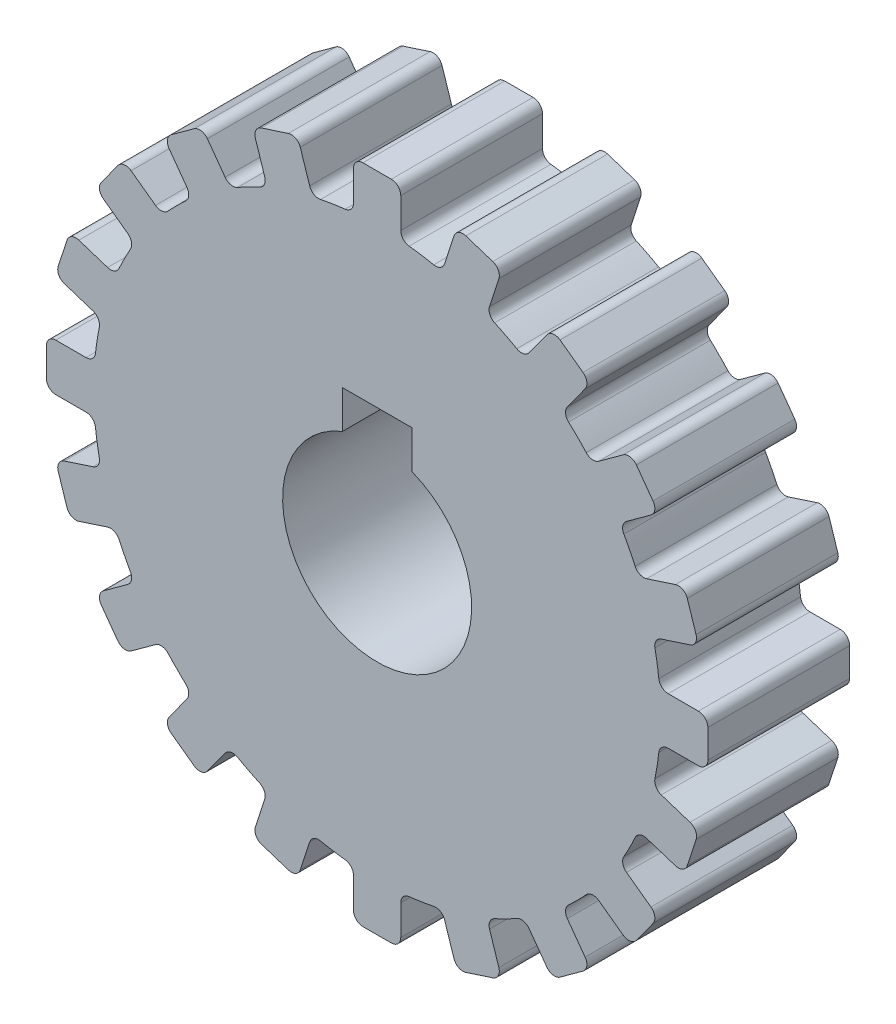
SolidWorks part; units mm, degrees
ref_plane "Front Plane" through (0, 0, 0) normal (0, 0, 1) x (1, 0, 0)
ref_plane "Top Plane" through (0, 0, 0) normal (0, 1, 0) x (1, 0, 0)
ref_plane "Right Plane" through (0, 0, 0) normal (1, 0, 0) x (0, 0, -1)
sketch "Sketch1" plane through (0, 0, 0) normal (0, 0, 1) x (1, 0, 0)
  line L0 (8.3248, 68.5416) -> (7.8409, 65.4868)
  line L1 (-1.5, 70) -> (1.5, 70)
  line L2 (2.5, 69) -> (2.5, 65.9071)
  line L3 (-2.5, 69) -> (-2.5, 65.9071)
  line L4 (9.4689, 69.3728) -> (12.4319, 68.9035)
  line L5 (13.2632, 67.7594) -> (12.7794, 64.7046)
  line L6 (18.9445, 66.3954) -> (17.9888, 63.4539)
  line L7 (20.2046, 67.0375) -> (23.0578, 66.1104)
  line L8 (23.6998, 64.8504) -> (22.7441, 61.9089)
  line L9 (29.0978, 62.6144) -> (27.6937, 59.8587)
  line L10 (30.4428, 63.0514) -> (33.1158, 61.6895)
  line L11 (33.5529, 60.3445) -> (32.1487, 57.5887)
  line L12 (38.5346, 57.2916) -> (36.7167, 54.7895)
  line L13 (39.9314, 57.5129) -> (42.3585, 55.7495)
  line L14 (42.5797, 54.3527) -> (40.7618, 51.8505)
  line L15 (47.0226, 50.5581) -> (44.8356, 48.3711)
  line L16 (48.4368, 50.5581) -> (50.5581, 48.4368)
  line L17 (50.5581, 47.0226) -> (48.3711, 44.8356)
  line L18 (54.3527, 42.5797) -> (51.8505, 40.7618)
  line L19 (55.7495, 42.3585) -> (57.5129, 39.9314)
  line L20 (57.2916, 38.5346) -> (54.7895, 36.7167)
  line L21 (60.3445, 33.5529) -> (57.5887, 32.1487)
  line L22 (61.6895, 33.1158) -> (63.0514, 30.4428)
  line L23 (62.6144, 29.0978) -> (59.8587, 27.6937)
  line L24 (64.8504, 23.6998) -> (61.9089, 22.7441)
  line L25 (66.1104, 23.0578) -> (67.0375, 20.2046)
  line L26 (66.3954, 18.9445) -> (63.4539, 17.9888)
  line L27 (67.7594, 13.2632) -> (64.7046, 12.7794)
  line L28 (68.9035, 12.4319) -> (69.3728, 9.4689)
  line L29 (68.5416, 8.3248) -> (65.4868, 7.8409)
  line L30 (69, 2.5) -> (65.9071, 2.5)
  line L31 (70, 1.5) -> (70, -1.5)
  line L32 (69, -2.5) -> (65.9071, -2.5)
  line L33 (68.5416, -8.3248) -> (65.4868, -7.8409)
  line L34 (69.3728, -9.4689) -> (68.9035, -12.4319)
  line L35 (67.7594, -13.2632) -> (64.7046, -12.7794)
  line L36 (66.3954, -18.9445) -> (63.4539, -17.9888)
  line L37 (67.0375, -20.2046) -> (66.1104, -23.0578)
  line L38 (64.8504, -23.6998) -> (61.9089, -22.7441)
  line L39 (62.6144, -29.0978) -> (59.8587, -27.6937)
  line L40 (63.0514, -30.4428) -> (61.6895, -33.1158)
  line L41 (60.3445, -33.5529) -> (57.5887, -32.1487)
  line L42 (57.2916, -38.5346) -> (54.7895, -36.7167)
  line L43 (57.5129, -39.9314) -> (55.7495, -42.3585)
  line L44 (54.3527, -42.5797) -> (51.8505, -40.7618)
  line L45 (50.5581, -47.0226) -> (48.3711, -44.8356)
  line L46 (50.5581, -48.4368) -> (48.4368, -50.5581)
  line L47 (47.0226, -50.5581) -> (44.8356, -48.3711)
  line L48 (42.5797, -54.3527) -> (40.7618, -51.8505)
  line L49 (42.3585, -55.7495) -> (39.9314, -57.5129)
  line L50 (38.5346, -57.2916) -> (36.7167, -54.7895)
  line L51 (33.5529, -60.3445) -> (32.1487, -57.5887)
  line L52 (33.1158, -61.6895) -> (30.4428, -63.0514)
  line L53 (29.0978, -62.6144) -> (27.6937, -59.8587)
  line L54 (23.6998, -64.8504) -> (22.7441, -61.9089)
  line L55 (23.0578, -66.1104) -> (20.2046, -67.0375)
  line L56 (18.9445, -66.3954) -> (17.9888, -63.4539)
  line L57 (13.2632, -67.7594) -> (12.7794, -64.7046)
  line L58 (12.4319, -68.9035) -> (9.4689, -69.3728)
  line L59 (8.3248, -68.5416) -> (7.8409, -65.4868)
  line L60 (2.5, -69) -> (2.5, -65.9071)
  line L61 (1.5, -70) -> (-1.5, -70)
  line L62 (-2.5, -69) -> (-2.5, -65.9071)
  line L63 (-8.3248, -68.5416) -> (-7.8409, -65.4868)
  line L64 (-9.4689, -69.3728) -> (-12.4319, -68.9035)
  line L65 (-13.2632, -67.7594) -> (-12.7794, -64.7046)
  line L66 (-18.9445, -66.3954) -> (-17.9888, -63.4539)
  line L67 (-20.2046, -67.0375) -> (-23.0578, -66.1104)
  line L68 (-23.6998, -64.8504) -> (-22.7441, -61.9089)
  line L69 (-29.0978, -62.6144) -> (-27.6937, -59.8587)
  line L70 (-30.4428, -63.0514) -> (-33.1158, -61.6895)
  line L71 (-33.5529, -60.3445) -> (-32.1487, -57.5887)
  line L72 (-38.5346, -57.2916) -> (-36.7167, -54.7895)
  line L73 (-39.9314, -57.5129) -> (-42.3585, -55.7495)
  line L74 (-42.5797, -54.3527) -> (-40.7618, -51.8505)
  line L75 (-47.0226, -50.5581) -> (-44.8356, -48.3711)
  line L76 (-48.4368, -50.5581) -> (-50.5581, -48.4368)
  line L77 (-50.5581, -47.0226) -> (-48.3711, -44.8356)
  line L78 (-54.3527, -42.5797) -> (-51.8505, -40.7618)
  line L79 (-55.7495, -42.3585) -> (-57.5129, -39.9314)
  line L80 (-57.2916, -38.5346) -> (-54.7895, -36.7167)
  line L81 (-60.3445, -33.5529) -> (-57.5887, -32.1487)
  line L82 (-61.6895, -33.1158) -> (-63.0514, -30.4428)
  line L83 (-62.6144, -29.0978) -> (-59.8587, -27.6937)
  line L84 (-64.8504, -23.6998) -> (-61.9089, -22.7441)
  line L85 (-66.1104, -23.0578) -> (-67.0375, -20.2046)
  line L86 (-66.3954, -18.9445) -> (-63.4539, -17.9888)
  line L87 (-67.7594, -13.2632) -> (-64.7046, -12.7794)
  line L88 (-68.9035, -12.4319) -> (-69.3728, -9.4689)
  line L89 (-68.5416, -8.3248) -> (-65.4868, -7.8409)
  line L90 (-69, -2.5) -> (-65.9071, -2.5)
  line L91 (-70, -1.5) -> (-70, 1.5)
  line L92 (-69, 2.5) -> (-65.9071, 2.5)
  line L93 (-68.5416, 8.3248) -> (-65.4868, 7.8409)
  line L94 (-69.3728, 9.4689) -> (-68.9035, 12.4319)
  line L95 (-67.7594, 13.2632) -> (-64.7046, 12.7794)
  line L96 (-66.3954, 18.9445) -> (-63.4539, 17.9888)
  line L97 (-67.0375, 20.2046) -> (-66.1104, 23.0578)
  line L98 (-64.8504, 23.6998) -> (-61.9089, 22.7441)
  line L99 (-62.6144, 29.0978) -> (-59.8587, 27.6937)
  line L100 (-63.0514, 30.4428) -> (-61.6895, 33.1158)
  line L101 (-60.3445, 33.5529) -> (-57.5887, 32.1487)
  line L102 (-57.2916, 38.5346) -> (-54.7895, 36.7167)
  line L103 (-57.5129, 39.9314) -> (-55.7495, 42.3585)
  line L104 (-54.3527, 42.5797) -> (-51.8505, 40.7618)
  line L105 (-50.5581, 47.0226) -> (-48.3711, 44.8356)
  line L106 (-50.5581, 48.4368) -> (-48.4368, 50.5581)
  line L107 (-47.0226, 50.5581) -> (-44.8356, 48.3711)
  line L108 (-42.5797, 54.3527) -> (-40.7618, 51.8505)
  line L109 (-42.3585, 55.7495) -> (-39.9314, 57.5129)
  line L110 (-38.5346, 57.2916) -> (-36.7167, 54.7895)
  line L111 (-33.5529, 60.3445) -> (-32.1487, 57.5887)
  line L112 (-33.1158, 61.6895) -> (-30.4428, 63.0514)
  line L113 (-29.0978, 62.6144) -> (-27.6937, 59.8587)
  line L114 (-23.6998, 64.8504) -> (-22.7441, 61.9089)
  line L115 (-23.0578, 66.1104) -> (-20.2046, 67.0375)
  line L116 (-18.9445, 66.3954) -> (-17.9888, 63.4539)
  line L117 (-13.2632, 67.7594) -> (-12.7794, 64.7046)
  line L118 (-12.4319, 68.9035) -> (-9.4689, 69.3728)
  line L119 (-8.3248, 68.5416) -> (-7.8409, 65.4868)
  arc A0 (-3.447, 64.9085) -> (-6.7494, 64.6486) centre (0, 0) ccw
  arc A2 (-2.5, 65.9071) -> (-3.447, 64.9085) centre (-3.5, 65.9071) cw
  arc A3 (3.447, 64.9085) -> (2.5, 65.9071) centre (3.5, 65.9071) cw
  arc A4 (1.5, 70) -> (2.5, 69) centre (1.5, 69) cw
  arc A5 (-1.5, 70) -> (-2.5, 69) centre (-1.5, 69) ccw
  arc A6 (7.8409, 65.4868) -> (6.7494, 64.6486) centre (6.8532, 65.6432) cw
  arc A7 (9.4689, 69.3728) -> (8.3248, 68.5416) centre (9.3124, 68.3851) ccw
  arc A8 (12.4319, 68.9035) -> (13.2632, 67.7594) centre (12.2755, 67.9158) cw
  arc A9 (13.5585, 63.5702) -> (12.7794, 64.7046) centre (13.7671, 64.5482) cw
  arc A10 (17.9888, 63.4539) -> (16.7796, 62.7969) centre (17.0377, 63.763) cw
  arc A11 (20.2046, 67.0375) -> (18.9445, 66.3954) centre (19.8956, 66.0864) ccw
  arc A12 (23.0578, 66.1104) -> (23.6998, 64.8504) centre (22.7488, 65.1594) cw
  arc A13 (23.3361, 60.6665) -> (22.7441, 61.9089) centre (23.6951, 61.5998) cw
  arc A14 (27.6937, 59.8587) -> (26.3966, 59.3988) centre (26.8027, 60.3127) cw
  arc A15 (30.4428, 63.0514) -> (29.0978, 62.6144) centre (29.9888, 62.1604) ccw
  arc A16 (33.1158, 61.6895) -> (33.5529, 60.3445) centre (32.6619, 60.7985) cw
  arc A17 (32.5391, 56.269) -> (32.1487, 57.5887) centre (33.0397, 57.1347) cw
  arc A18 (36.7167, 54.7895) -> (35.3636, 54.5382) centre (35.9077, 55.3772) cw
  arc A19 (39.9314, 57.5129) -> (38.5346, 57.2916) centre (39.3437, 56.7039) ccw
  arc A20 (42.3585, 55.7495) -> (42.5797, 54.3527) centre (41.7707, 54.9405) cw
  arc A21 (40.9409, 50.486) -> (40.7618, 51.8505) centre (41.5708, 51.2627) cw
  arc A22 (44.8356, 48.3711) -> (43.4599, 48.3346) centre (44.1285, 49.0783) cw
  arc A23 (48.4368, 50.5581) -> (47.0226, 50.5581) centre (47.7297, 49.851) ccw
  arc A24 (50.5581, 48.4368) -> (50.5581, 47.0226) centre (49.851, 47.7297) cw
  arc A25 (48.3346, 43.4599) -> (48.3711, 44.8356) centre (49.0783, 44.1285) cw
  arc A26 (51.8505, 40.7618) -> (50.486, 40.9409) centre (51.2627, 41.5708) cw
  arc A27 (55.7495, 42.3585) -> (54.3527, 42.5797) centre (54.9405, 41.7707) ccw
  arc A28 (57.5129, 39.9314) -> (57.2916, 38.5346) centre (56.7039, 39.3437) cw
  arc A29 (54.5382, 35.3636) -> (54.7895, 36.7167) centre (55.3772, 35.9077) cw
  arc A30 (57.5887, 32.1487) -> (56.269, 32.5391) centre (57.1347, 33.0397) cw
  arc A31 (61.6895, 33.1158) -> (60.3445, 33.5529) centre (60.7985, 32.6619) ccw
  arc A32 (63.0514, 30.4428) -> (62.6144, 29.0978) centre (62.1604, 29.9888) cw
  arc A33 (59.3988, 26.3966) -> (59.8587, 27.6937) centre (60.3127, 26.8027) cw
  arc A34 (61.9089, 22.7441) -> (60.6665, 23.3361) centre (61.5998, 23.6951) cw
  arc A35 (66.1104, 23.0578) -> (64.8504, 23.6998) centre (65.1594, 22.7488) ccw
  arc A36 (67.0375, 20.2046) -> (66.3954, 18.9445) centre (66.0864, 19.8956) cw
  arc A37 (62.7969, 16.7796) -> (63.4539, 17.9888) centre (63.763, 17.0377) cw
  arc A38 (64.7046, 12.7794) -> (63.5702, 13.5585) centre (64.5482, 13.7671) cw
  arc A39 (68.9035, 12.4319) -> (67.7594, 13.2632) centre (67.9158, 12.2755) ccw
  arc A40 (69.3728, 9.4689) -> (68.5416, 8.3248) centre (68.3851, 9.3124) cw
  arc A41 (64.6486, 6.7494) -> (65.4868, 7.8409) centre (65.6432, 6.8532) cw
  arc A42 (65.9071, 2.5) -> (64.9085, 3.447) centre (65.9071, 3.5) cw
  arc A43 (70, 1.5) -> (69, 2.5) centre (69, 1.5) ccw
  arc A44 (70, -1.5) -> (69, -2.5) centre (69, -1.5) cw
  arc A45 (64.9085, -3.447) -> (65.9071, -2.5) centre (65.9071, -3.5) cw
  arc A46 (65.4868, -7.8409) -> (64.6486, -6.7494) centre (65.6432, -6.8532) cw
  arc A47 (69.3728, -9.4689) -> (68.5416, -8.3248) centre (68.3851, -9.3124) ccw
  arc A48 (68.9035, -12.4319) -> (67.7594, -13.2632) centre (67.9158, -12.2755) cw
  arc A49 (63.5702, -13.5585) -> (64.7046, -12.7794) centre (64.5482, -13.7671) cw
  arc A50 (63.4539, -17.9888) -> (62.7969, -16.7796) centre (63.763, -17.0377) cw
  arc A51 (67.0375, -20.2046) -> (66.3954, -18.9445) centre (66.0864, -19.8956) ccw
  arc A52 (66.1104, -23.0578) -> (64.8504, -23.6998) centre (65.1594, -22.7488) cw
  arc A53 (60.6665, -23.3361) -> (61.9089, -22.7441) centre (61.5998, -23.6951) cw
  arc A54 (59.8587, -27.6937) -> (59.3988, -26.3966) centre (60.3127, -26.8027) cw
  arc A55 (63.0514, -30.4428) -> (62.6144, -29.0978) centre (62.1604, -29.9888) ccw
  arc A56 (61.6895, -33.1158) -> (60.3445, -33.5529) centre (60.7985, -32.6619) cw
  arc A57 (56.269, -32.5391) -> (57.5887, -32.1487) centre (57.1347, -33.0397) cw
  arc A58 (54.7895, -36.7167) -> (54.5382, -35.3636) centre (55.3772, -35.9077) cw
  arc A59 (57.5129, -39.9314) -> (57.2916, -38.5346) centre (56.7039, -39.3437) ccw
  arc A60 (55.7495, -42.3585) -> (54.3527, -42.5797) centre (54.9405, -41.7707) cw
  arc A61 (50.486, -40.9409) -> (51.8505, -40.7618) centre (51.2627, -41.5708) cw
  arc A62 (48.3711, -44.8356) -> (48.3346, -43.4599) centre (49.0783, -44.1285) cw
  arc A63 (50.5581, -48.4368) -> (50.5581, -47.0226) centre (49.851, -47.7297) ccw
  arc A64 (48.4368, -50.5581) -> (47.0226, -50.5581) centre (47.7297, -49.851) cw
  arc A65 (43.4599, -48.3346) -> (44.8356, -48.3711) centre (44.1285, -49.0783) cw
  arc A66 (40.7618, -51.8505) -> (40.9409, -50.486) centre (41.5708, -51.2627) cw
  arc A67 (42.3585, -55.7495) -> (42.5797, -54.3527) centre (41.7707, -54.9405) ccw
  arc A68 (39.9314, -57.5129) -> (38.5346, -57.2916) centre (39.3437, -56.7039) cw
  arc A69 (35.3636, -54.5382) -> (36.7167, -54.7895) centre (35.9077, -55.3772) cw
  arc A70 (32.1487, -57.5887) -> (32.5391, -56.269) centre (33.0397, -57.1347) cw
  arc A71 (33.1158, -61.6895) -> (33.5529, -60.3445) centre (32.6619, -60.7985) ccw
  arc A72 (30.4428, -63.0514) -> (29.0978, -62.6144) centre (29.9888, -62.1604) cw
  arc A73 (26.3966, -59.3988) -> (27.6937, -59.8587) centre (26.8027, -60.3127) cw
  arc A74 (22.7441, -61.9089) -> (23.3361, -60.6665) centre (23.6951, -61.5998) cw
  arc A75 (23.0578, -66.1104) -> (23.6998, -64.8504) centre (22.7488, -65.1594) ccw
  arc A76 (20.2046, -67.0375) -> (18.9445, -66.3954) centre (19.8956, -66.0864) cw
  arc A77 (16.7796, -62.7969) -> (17.9888, -63.4539) centre (17.0377, -63.763) cw
  arc A78 (12.7794, -64.7046) -> (13.5585, -63.5702) centre (13.7671, -64.5482) cw
  arc A79 (12.4319, -68.9035) -> (13.2632, -67.7594) centre (12.2755, -67.9158) ccw
  arc A80 (9.4689, -69.3728) -> (8.3248, -68.5416) centre (9.3124, -68.3851) cw
  arc A81 (6.7494, -64.6486) -> (7.8409, -65.4868) centre (6.8532, -65.6432) cw
  arc A82 (2.5, -65.9071) -> (3.447, -64.9085) centre (3.5, -65.9071) cw
  arc A83 (1.5, -70) -> (2.5, -69) centre (1.5, -69) ccw
  arc A84 (-1.5, -70) -> (-2.5, -69) centre (-1.5, -69) cw
  arc A85 (-3.447, -64.9085) -> (-2.5, -65.9071) centre (-3.5, -65.9071) cw
  arc A86 (-7.8409, -65.4868) -> (-6.7494, -64.6486) centre (-6.8532, -65.6432) cw
  arc A87 (-9.4689, -69.3728) -> (-8.3248, -68.5416) centre (-9.3124, -68.3851) ccw
  arc A88 (-12.4319, -68.9035) -> (-13.2632, -67.7594) centre (-12.2755, -67.9158) cw
  arc A89 (-13.5585, -63.5702) -> (-12.7794, -64.7046) centre (-13.7671, -64.5482) cw
  arc A90 (-17.9888, -63.4539) -> (-16.7796, -62.7969) centre (-17.0377, -63.763) cw
  arc A91 (-20.2046, -67.0375) -> (-18.9445, -66.3954) centre (-19.8956, -66.0864) ccw
  arc A92 (-23.0578, -66.1104) -> (-23.6998, -64.8504) centre (-22.7488, -65.1594) cw
  arc A93 (-23.3361, -60.6665) -> (-22.7441, -61.9089) centre (-23.6951, -61.5998) cw
  arc A94 (-27.6937, -59.8587) -> (-26.3966, -59.3988) centre (-26.8027, -60.3127) cw
  arc A95 (-30.4428, -63.0514) -> (-29.0978, -62.6144) centre (-29.9888, -62.1604) ccw
  arc A96 (-33.1158, -61.6895) -> (-33.5529, -60.3445) centre (-32.6619, -60.7985) cw
  arc A97 (-32.5391, -56.269) -> (-32.1487, -57.5887) centre (-33.0397, -57.1347) cw
  arc A98 (-36.7167, -54.7895) -> (-35.3636, -54.5382) centre (-35.9077, -55.3772) cw
  arc A99 (-39.9314, -57.5129) -> (-38.5346, -57.2916) centre (-39.3437, -56.7039) ccw
  arc A100 (-42.3585, -55.7495) -> (-42.5797, -54.3527) centre (-41.7707, -54.9405) cw
  arc A101 (-40.9409, -50.486) -> (-40.7618, -51.8505) centre (-41.5708, -51.2627) cw
  arc A102 (-44.8356, -48.3711) -> (-43.4599, -48.3346) centre (-44.1285, -49.0783) cw
  arc A103 (-48.4368, -50.5581) -> (-47.0226, -50.5581) centre (-47.7297, -49.851) ccw
  arc A104 (-50.5581, -48.4368) -> (-50.5581, -47.0226) centre (-49.851, -47.7297) cw
  arc A105 (-48.3346, -43.4599) -> (-48.3711, -44.8356) centre (-49.0783, -44.1285) cw
  arc A106 (-51.8505, -40.7618) -> (-50.486, -40.9409) centre (-51.2627, -41.5708) cw
  arc A107 (-55.7495, -42.3585) -> (-54.3527, -42.5797) centre (-54.9405, -41.7707) ccw
  arc A108 (-57.5129, -39.9314) -> (-57.2916, -38.5346) centre (-56.7039, -39.3437) cw
  arc A109 (-54.5382, -35.3636) -> (-54.7895, -36.7167) centre (-55.3772, -35.9077) cw
  arc A110 (-57.5887, -32.1487) -> (-56.269, -32.5391) centre (-57.1347, -33.0397) cw
  arc A111 (-61.6895, -33.1158) -> (-60.3445, -33.5529) centre (-60.7985, -32.6619) ccw
  arc A112 (-63.0514, -30.4428) -> (-62.6144, -29.0978) centre (-62.1604, -29.9888) cw
  arc A113 (-59.3988, -26.3966) -> (-59.8587, -27.6937) centre (-60.3127, -26.8027) cw
  arc A114 (-61.9089, -22.7441) -> (-60.6665, -23.3361) centre (-61.5998, -23.6951) cw
  arc A115 (-66.1104, -23.0578) -> (-64.8504, -23.6998) centre (-65.1594, -22.7488) ccw
  arc A116 (-67.0375, -20.2046) -> (-66.3954, -18.9445) centre (-66.0864, -19.8956) cw
  arc A117 (-62.7969, -16.7796) -> (-63.4539, -17.9888) centre (-63.763, -17.0377) cw
  arc A118 (-64.7046, -12.7794) -> (-63.5702, -13.5585) centre (-64.5482, -13.7671) cw
  arc A119 (-68.9035, -12.4319) -> (-67.7594, -13.2632) centre (-67.9158, -12.2755) ccw
  arc A120 (-69.3728, -9.4689) -> (-68.5416, -8.3248) centre (-68.3851, -9.3124) cw
  arc A121 (-64.6486, -6.7494) -> (-65.4868, -7.8409) centre (-65.6432, -6.8532) cw
  arc A122 (-65.9071, -2.5) -> (-64.9085, -3.447) centre (-65.9071, -3.5) cw
  arc A123 (-70, -1.5) -> (-69, -2.5) centre (-69, -1.5) ccw
  arc A124 (-70, 1.5) -> (-69, 2.5) centre (-69, 1.5) cw
  arc A125 (-64.9085, 3.447) -> (-65.9071, 2.5) centre (-65.9071, 3.5) cw
  arc A126 (-65.4868, 7.8409) -> (-64.6486, 6.7494) centre (-65.6432, 6.8532) cw
  arc A127 (-69.3728, 9.4689) -> (-68.5416, 8.3248) centre (-68.3851, 9.3124) ccw
  arc A128 (-68.9035, 12.4319) -> (-67.7594, 13.2632) centre (-67.9158, 12.2755) cw
  arc A129 (-63.5702, 13.5585) -> (-64.7046, 12.7794) centre (-64.5482, 13.7671) cw
  arc A130 (-63.4539, 17.9888) -> (-62.7969, 16.7796) centre (-63.763, 17.0377) cw
  arc A131 (-67.0375, 20.2046) -> (-66.3954, 18.9445) centre (-66.0864, 19.8956) ccw
  arc A132 (-66.1104, 23.0578) -> (-64.8504, 23.6998) centre (-65.1594, 22.7488) cw
  arc A133 (-60.6665, 23.3361) -> (-61.9089, 22.7441) centre (-61.5998, 23.6951) cw
  arc A134 (-59.8587, 27.6937) -> (-59.3988, 26.3966) centre (-60.3127, 26.8027) cw
  arc A135 (-63.0514, 30.4428) -> (-62.6144, 29.0978) centre (-62.1604, 29.9888) ccw
  arc A136 (-61.6895, 33.1158) -> (-60.3445, 33.5529) centre (-60.7985, 32.6619) cw
  arc A137 (-56.269, 32.5391) -> (-57.5887, 32.1487) centre (-57.1347, 33.0397) cw
  arc A138 (-54.7895, 36.7167) -> (-54.5382, 35.3636) centre (-55.3772, 35.9077) cw
  arc A139 (-57.5129, 39.9314) -> (-57.2916, 38.5346) centre (-56.7039, 39.3437) ccw
  arc A140 (-55.7495, 42.3585) -> (-54.3527, 42.5797) centre (-54.9405, 41.7707) cw
  arc A141 (-50.486, 40.9409) -> (-51.8505, 40.7618) centre (-51.2627, 41.5708) cw
  arc A142 (-48.3711, 44.8356) -> (-48.3346, 43.4599) centre (-49.0783, 44.1285) cw
  arc A143 (-50.5581, 48.4368) -> (-50.5581, 47.0226) centre (-49.851, 47.7297) ccw
  arc A144 (-48.4368, 50.5581) -> (-47.0226, 50.5581) centre (-47.7297, 49.851) cw
  arc A145 (-43.4599, 48.3346) -> (-44.8356, 48.3711) centre (-44.1285, 49.0783) cw
  arc A146 (-40.7618, 51.8505) -> (-40.9409, 50.486) centre (-41.5708, 51.2627) cw
  arc A147 (-42.3585, 55.7495) -> (-42.5797, 54.3527) centre (-41.7707, 54.9405) ccw
  arc A148 (-39.9314, 57.5129) -> (-38.5346, 57.2916) centre (-39.3437, 56.7039) cw
  arc A149 (-35.3636, 54.5382) -> (-36.7167, 54.7895) centre (-35.9077, 55.3772) cw
  arc A150 (-32.1487, 57.5887) -> (-32.5391, 56.269) centre (-33.0397, 57.1347) cw
  arc A151 (-33.1158, 61.6895) -> (-33.5529, 60.3445) centre (-32.6619, 60.7985) ccw
  arc A152 (-30.4428, 63.0514) -> (-29.0978, 62.6144) centre (-29.9888, 62.1604) cw
  arc A153 (-26.3966, 59.3988) -> (-27.6937, 59.8587) centre (-26.8027, 60.3127) cw
  arc A154 (-22.7441, 61.9089) -> (-23.3361, 60.6665) centre (-23.6951, 61.5998) cw
  arc A155 (-23.0578, 66.1104) -> (-23.6998, 64.8504) centre (-22.7488, 65.1594) ccw
  arc A156 (-20.2046, 67.0375) -> (-18.9445, 66.3954) centre (-19.8956, 66.0864) cw
  arc A157 (-16.7796, 62.7969) -> (-17.9888, 63.4539) centre (-17.0377, 63.763) cw
  arc A158 (-12.7794, 64.7046) -> (-13.5585, 63.5702) centre (-13.7671, 64.5482) cw
  arc A159 (-12.4319, 68.9035) -> (-13.2632, 67.7594) centre (-12.2755, 67.9158) ccw
  arc A160 (-9.4689, 69.3728) -> (-8.3248, 68.5416) centre (-9.3124, 68.3851) cw
  arc A161 (-6.7494, 64.6486) -> (-7.8409, 65.4868) centre (-6.8532, 65.6432) cw
  arc A162 (-13.5585, 63.5702) -> (-16.7796, 62.7969) centre (0, 0) ccw
  arc A163 (6.7494, 64.6486) -> (3.447, 64.9085) centre (0, 0) ccw
  arc A164 (16.7796, 62.7969) -> (13.5585, 63.5702) centre (0, 0) ccw
  arc A165 (26.3966, 59.3988) -> (23.3361, 60.6665) centre (0, 0) ccw
  arc A166 (-23.3361, 60.6665) -> (-26.3966, 59.3988) centre (0, 0) ccw
  arc A167 (-32.5391, 56.269) -> (-35.3636, 54.5382) centre (0, 0) ccw
  arc A168 (-40.9409, 50.486) -> (-43.4599, 48.3346) centre (0, 0) ccw
  arc A169 (-48.3346, 43.4599) -> (-50.486, 40.9409) centre (0, 0) ccw
  arc A170 (-54.5382, 35.3636) -> (-56.269, 32.5391) centre (0, 0) ccw
  arc A171 (35.3636, 54.5382) -> (32.5391, 56.269) centre (0, 0) ccw
  arc A172 (43.4599, 48.3346) -> (40.9409, 50.486) centre (0, 0) ccw
  arc A173 (50.486, 40.9409) -> (48.3346, 43.4599) centre (0, 0) ccw
  arc A174 (56.269, 32.5391) -> (54.5382, 35.3636) centre (0, 0) ccw
  arc A175 (60.6665, 23.3361) -> (59.3988, 26.3966) centre (0, 0) ccw
  arc A176 (63.5702, 13.5585) -> (62.7969, 16.7796) centre (0, 0) ccw
  arc A177 (64.9085, 3.447) -> (64.6486, 6.7494) centre (0, 0) ccw
  arc A178 (64.6486, -6.7494) -> (64.9085, -3.447) centre (0, 0) ccw
  arc A179 (62.7969, -16.7796) -> (63.5702, -13.5585) centre (0, 0) ccw
  arc A180 (59.3988, -26.3966) -> (60.6665, -23.3361) centre (0, 0) ccw
  arc A181 (54.5382, -35.3636) -> (56.269, -32.5391) centre (0, 0) ccw
  arc A182 (48.3346, -43.4599) -> (50.486, -40.9409) centre (0, 0) ccw
  arc A183 (40.9409, -50.486) -> (43.4599, -48.3346) centre (0, 0) ccw
  arc A184 (32.5391, -56.269) -> (35.3636, -54.5382) centre (0, 0) ccw
  arc A185 (23.3361, -60.6665) -> (26.3966, -59.3988) centre (0, 0) ccw
  arc A186 (13.5585, -63.5702) -> (16.7796, -62.7969) centre (0, 0) ccw
  arc A187 (3.447, -64.9085) -> (6.7494, -64.6486) centre (0, 0) ccw
  arc A188 (-6.7494, -64.6486) -> (-3.447, -64.9085) centre (0, 0) ccw
  arc A189 (-16.7796, -62.7969) -> (-13.5585, -63.5702) centre (0, 0) ccw
  arc A190 (-26.3966, -59.3988) -> (-23.3361, -60.6665) centre (0, 0) ccw
  arc A191 (-35.3636, -54.5382) -> (-32.5391, -56.269) centre (0, 0) ccw
  arc A192 (-43.4599, -48.3346) -> (-40.9409, -50.486) centre (0, 0) ccw
  arc A193 (-50.486, -40.9409) -> (-48.3346, -43.4599) centre (0, 0) ccw
  arc A194 (-56.269, -32.5391) -> (-54.5382, -35.3636) centre (0, 0) ccw
  arc A195 (-60.6665, -23.3361) -> (-59.3988, -26.3966) centre (0, 0) ccw
  arc A196 (-63.5702, -13.5585) -> (-62.7969, -16.7796) centre (0, 0) ccw
  arc A197 (-64.9085, -3.447) -> (-64.6486, -6.7494) centre (0, 0) ccw
  arc A198 (-64.6486, 6.7494) -> (-64.9085, 3.447) centre (0, 0) ccw
  arc A199 (-62.7969, 16.7796) -> (-63.5702, 13.5585) centre (0, 0) ccw
  arc A200 (-59.3988, 26.3966) -> (-60.6665, 23.3361) centre (0, 0) ccw
  point P486 (0, 0)
  dimension "D1" = 1
  dimension "D2" = 40
extrude "Boss-Extrude1" add sketch "Sketch1" along normal blind 30
sketch "Sketch2" plane through (0, 0, 30) normal (0, 0, 1) x (1, 0, 0)
  line L1 (-3.5387, 13.1147) -> (3.5387, 13.1147)
  line L2 (-3.5387, 13.1147) -> (-3.5387, 9.353)
  line L4 (3.5387, 13.1147) -> (3.5387, 9.353)
  circle A0 centre (0, 0) radius 20
  arc A1 (-3.5387, 9.353) -> (3.5387, 9.353) centre (0, 0) ccw
extrude "Cut-Extrude1" cut sketch "Sketch2" against normal blind 30 contours A1 L4 L1 L2
sketch "Sketch3" plane through (0, 0, 30) normal (0, 0, 1) x (1, 0, 0)
  circle A0 centre (0, 0) radius 20
  circle A1 centre (0, 0) radius 54.3215
extrude "Cut-Extrude2" cut sketch "Sketch3" against normal blind 15
fillet "Fillet2" radius 1 1 edges at (54.3215, 0, 30)
sketch "Sketch4" plane through (0, 0, 30) normal (0, 0, 1) x (1, 0, 0)
  line L0 (8.1289, 33.1085) -> (7.1406, 30.0668)
  line L1 (-1.5, 35) -> (1.5, 35)
  line L2 (2.5, 34) -> (2.5, 30.8018)
  line L3 (-2.5, 34) -> (-2.5, 30.8018)
  line L4 (9.389, 33.7505) -> (12.2422, 32.8235)
  line L5 (12.8842, 31.5634) -> (11.8959, 28.5217)
  line L6 (17.9622, 28.976) -> (16.0823, 26.3886)
  line L7 (19.359, 29.1973) -> (21.786, 27.4339)
  line L8 (22.0072, 26.0371) -> (20.1274, 23.4497)
  line L9 (26.0371, 22.0072) -> (23.4497, 20.1274)
  line L10 (27.4339, 21.786) -> (29.1973, 19.359)
  line L11 (28.976, 17.9622) -> (26.3886, 16.0823)
  line L12 (31.5634, 12.8842) -> (28.5217, 11.8959)
  line L13 (32.8235, 12.2422) -> (33.7505, 9.389)
  line L14 (33.1085, 8.1289) -> (30.0668, 7.1406)
  line L15 (34, 2.5) -> (30.8018, 2.5)
  line L16 (35, 1.5) -> (35, -1.5)
  line L17 (34, -2.5) -> (30.8018, -2.5)
  line L18 (33.1085, -8.1289) -> (30.0668, -7.1406)
  line L19 (33.7505, -9.389) -> (32.8235, -12.2422)
  line L20 (31.5634, -12.8842) -> (28.5217, -11.8959)
  line L21 (28.976, -17.9622) -> (26.3886, -16.0823)
  line L22 (29.1973, -19.359) -> (27.4339, -21.786)
  line L23 (26.0371, -22.0072) -> (23.4497, -20.1274)
  line L24 (22.0072, -26.0371) -> (20.1274, -23.4497)
  line L25 (21.786, -27.4339) -> (19.359, -29.1973)
  line L26 (17.9622, -28.976) -> (16.0823, -26.3886)
  line L27 (12.8842, -31.5634) -> (11.8959, -28.5217)
  line L28 (12.2422, -32.8235) -> (9.389, -33.7505)
  line L29 (8.1289, -33.1085) -> (7.1406, -30.0668)
  line L30 (2.5, -34) -> (2.5, -30.8018)
  line L31 (1.5, -35) -> (-1.5, -35)
  line L32 (-2.5, -34) -> (-2.5, -30.8018)
  line L33 (-8.1289, -33.1085) -> (-7.1406, -30.0668)
  line L34 (-9.389, -33.7505) -> (-12.2422, -32.8235)
  line L35 (-12.8842, -31.5634) -> (-11.8959, -28.5217)
  line L36 (-17.9622, -28.976) -> (-16.0823, -26.3886)
  line L37 (-19.359, -29.1973) -> (-21.786, -27.4339)
  line L38 (-22.0072, -26.0371) -> (-20.1274, -23.4497)
  line L39 (-26.0371, -22.0072) -> (-23.4497, -20.1274)
  line L40 (-27.4339, -21.786) -> (-29.1973, -19.359)
  line L41 (-28.976, -17.9622) -> (-26.3886, -16.0823)
  line L42 (-31.5634, -12.8842) -> (-28.5217, -11.8959)
  line L43 (-32.8235, -12.2422) -> (-33.7505, -9.389)
  line L44 (-33.1085, -8.1289) -> (-30.0668, -7.1406)
  line L45 (-34, -2.5) -> (-30.8018, -2.5)
  line L46 (-35, -1.5) -> (-35, 1.5)
  line L47 (-34, 2.5) -> (-30.8018, 2.5)
  line L48 (-33.1085, 8.1289) -> (-30.0668, 7.1406)
  line L49 (-33.7505, 9.389) -> (-32.8235, 12.2422)
  line L50 (-31.5634, 12.8842) -> (-28.5217, 11.8959)
  line L51 (-28.976, 17.9622) -> (-26.3886, 16.0823)
  line L52 (-29.1973, 19.359) -> (-27.4339, 21.786)
  line L53 (-26.0371, 22.0072) -> (-23.4497, 20.1274)
  line L54 (-22.0072, 26.0371) -> (-20.1274, 23.4497)
  line L55 (-21.786, 27.4339) -> (-19.359, 29.1973)
  line L56 (-17.9622, 28.976) -> (-16.0823, 26.3886)
  line L57 (-12.8842, 31.5634) -> (-11.8959, 28.5217)
  line L58 (-12.2422, 32.8235) -> (-9.389, 33.7505)
  line L59 (-8.1289, 33.1085) -> (-7.1406, 30.0668)
  arc A0 (-3.3871, 29.8082) -> (-5.9899, 29.3959) centre (0, 0) ccw
  arc A2 (2.5, 30.8018) -> (3.3871, 29.8082) centre (3.5, 30.8018) ccw
  arc A3 (2.5, 34) -> (1.5, 35) centre (1.5, 34) ccw
  arc A4 (-1.5, 35) -> (-2.5, 34) centre (-1.5, 34) ccw
  arc A5 (-2.5, 30.8018) -> (-3.3871, 29.8082) centre (-3.5, 30.8018) cw
  arc A6 (7.1406, 30.0668) -> (5.9899, 29.3959) centre (6.1896, 30.3758) cw
  arc A7 (9.389, 33.7505) -> (8.1289, 33.1085) centre (9.08, 32.7994) ccw
  arc A8 (12.8842, 31.5634) -> (12.2422, 32.8235) centre (11.9332, 31.8724) ccw
  arc A9 (11.8959, 28.5217) -> (12.4326, 27.3026) centre (12.847, 28.2127) ccw
  arc A10 (16.0823, 26.3886) -> (14.7806, 26.1062) centre (15.2733, 26.9764) cw
  arc A11 (19.359, 29.1973) -> (17.9622, 28.976) centre (18.7712, 28.3883) ccw
  arc A12 (22.0072, 26.0371) -> (21.786, 27.4339) centre (21.1982, 26.6249) ccw
  arc A13 (20.1274, 23.4497) -> (20.261, 22.1244) centre (20.9364, 22.8619) ccw
  arc A14 (23.4497, 20.1274) -> (22.1244, 20.261) centre (22.8619, 20.9364) cw
  arc A15 (27.4339, 21.786) -> (26.0371, 22.0072) centre (26.6249, 21.1982) ccw
  arc A16 (28.976, 17.9622) -> (29.1973, 19.359) centre (28.3883, 18.7712) ccw
  arc A17 (26.3886, 16.0823) -> (26.1062, 14.7806) centre (26.9764, 15.2733) ccw
  arc A18 (28.5217, 11.8959) -> (27.3026, 12.4326) centre (28.2127, 12.847) cw
  arc A19 (32.8235, 12.2422) -> (31.5634, 12.8842) centre (31.8724, 11.9332) ccw
  arc A20 (33.1085, 8.1289) -> (33.7505, 9.389) centre (32.7994, 9.08) ccw
  arc A21 (30.0668, 7.1406) -> (29.3959, 5.9899) centre (30.3758, 6.1896) ccw
  arc A22 (30.8018, 2.5) -> (29.8082, 3.3871) centre (30.8018, 3.5) cw
  arc A23 (35, 1.5) -> (34, 2.5) centre (34, 1.5) ccw
  arc A24 (34, -2.5) -> (35, -1.5) centre (34, -1.5) ccw
  arc A25 (30.8018, -2.5) -> (29.8082, -3.3871) centre (30.8018, -3.5) ccw
  arc A26 (30.0668, -7.1406) -> (29.3959, -5.9899) centre (30.3758, -6.1896) cw
  arc A27 (33.7505, -9.389) -> (33.1085, -8.1289) centre (32.7994, -9.08) ccw
  arc A28 (31.5634, -12.8842) -> (32.8235, -12.2422) centre (31.8724, -11.9332) ccw
  arc A29 (28.5217, -11.8959) -> (27.3026, -12.4326) centre (28.2127, -12.847) ccw
  arc A30 (26.3886, -16.0823) -> (26.1062, -14.7806) centre (26.9764, -15.2733) cw
  arc A31 (29.1973, -19.359) -> (28.976, -17.9622) centre (28.3883, -18.7712) ccw
  arc A32 (26.0371, -22.0072) -> (27.4339, -21.786) centre (26.6249, -21.1982) ccw
  arc A33 (23.4497, -20.1274) -> (22.1244, -20.261) centre (22.8619, -20.9364) ccw
  arc A34 (20.1274, -23.4497) -> (20.261, -22.1244) centre (20.9364, -22.8619) cw
  arc A35 (21.786, -27.4339) -> (22.0072, -26.0371) centre (21.1982, -26.6249) ccw
  arc A36 (17.9622, -28.976) -> (19.359, -29.1973) centre (18.7712, -28.3883) ccw
  arc A37 (16.0823, -26.3886) -> (14.7806, -26.1062) centre (15.2733, -26.9764) ccw
  arc A38 (11.8959, -28.5217) -> (12.4326, -27.3026) centre (12.847, -28.2127) cw
  arc A39 (12.2422, -32.8235) -> (12.8842, -31.5634) centre (11.9332, -31.8724) ccw
  arc A40 (8.1289, -33.1085) -> (9.389, -33.7505) centre (9.08, -32.7994) ccw
  arc A41 (7.1406, -30.0668) -> (5.9899, -29.3959) centre (6.1896, -30.3758) ccw
  arc A42 (2.5, -30.8018) -> (3.3871, -29.8082) centre (3.5, -30.8018) cw
  arc A43 (1.5, -35) -> (2.5, -34) centre (1.5, -34) ccw
  arc A44 (-2.5, -34) -> (-1.5, -35) centre (-1.5, -34) ccw
  arc A45 (-2.5, -30.8018) -> (-3.3871, -29.8082) centre (-3.5, -30.8018) ccw
  arc A46 (-7.1406, -30.0668) -> (-5.9899, -29.3959) centre (-6.1896, -30.3758) cw
  arc A47 (-9.389, -33.7505) -> (-8.1289, -33.1085) centre (-9.08, -32.7994) ccw
  arc A48 (-12.8842, -31.5634) -> (-12.2422, -32.8235) centre (-11.9332, -31.8724) ccw
  arc A49 (-11.8959, -28.5217) -> (-12.4326, -27.3026) centre (-12.847, -28.2127) ccw
  arc A50 (-16.0823, -26.3886) -> (-14.7806, -26.1062) centre (-15.2733, -26.9764) cw
  arc A51 (-19.359, -29.1973) -> (-17.9622, -28.976) centre (-18.7712, -28.3883) ccw
  arc A52 (-22.0072, -26.0371) -> (-21.786, -27.4339) centre (-21.1982, -26.6249) ccw
  arc A53 (-20.1274, -23.4497) -> (-20.261, -22.1244) centre (-20.9364, -22.8619) ccw
  arc A54 (-23.4497, -20.1274) -> (-22.1244, -20.261) centre (-22.8619, -20.9364) cw
  arc A55 (-27.4339, -21.786) -> (-26.0371, -22.0072) centre (-26.6249, -21.1982) ccw
  arc A56 (-28.976, -17.9622) -> (-29.1973, -19.359) centre (-28.3883, -18.7712) ccw
  arc A57 (-26.3886, -16.0823) -> (-26.1062, -14.7806) centre (-26.9764, -15.2733) ccw
  arc A58 (-28.5217, -11.8959) -> (-27.3026, -12.4326) centre (-28.2127, -12.847) cw
  arc A59 (-32.8235, -12.2422) -> (-31.5634, -12.8842) centre (-31.8724, -11.9332) ccw
  arc A60 (-33.1085, -8.1289) -> (-33.7505, -9.389) centre (-32.7994, -9.08) ccw
  arc A61 (-30.0668, -7.1406) -> (-29.3959, -5.9899) centre (-30.3758, -6.1896) ccw
  arc A62 (-30.8018, -2.5) -> (-29.8082, -3.3871) centre (-30.8018, -3.5) cw
  arc A63 (-35, -1.5) -> (-34, -2.5) centre (-34, -1.5) ccw
  arc A64 (-34, 2.5) -> (-35, 1.5) centre (-34, 1.5) ccw
  arc A65 (-30.8018, 2.5) -> (-29.8082, 3.3871) centre (-30.8018, 3.5) ccw
  arc A66 (-30.0668, 7.1406) -> (-29.3959, 5.9899) centre (-30.3758, 6.1896) cw
  arc A67 (-33.7505, 9.389) -> (-33.1085, 8.1289) centre (-32.7994, 9.08) ccw
  arc A68 (-31.5634, 12.8842) -> (-32.8235, 12.2422) centre (-31.8724, 11.9332) ccw
  arc A69 (-28.5217, 11.8959) -> (-27.3026, 12.4326) centre (-28.2127, 12.847) ccw
  arc A70 (-26.3886, 16.0823) -> (-26.1062, 14.7806) centre (-26.9764, 15.2733) cw
  arc A71 (-29.1973, 19.359) -> (-28.976, 17.9622) centre (-28.3883, 18.7712) ccw
  arc A72 (-26.0371, 22.0072) -> (-27.4339, 21.786) centre (-26.6249, 21.1982) ccw
  arc A73 (-23.4497, 20.1274) -> (-22.1244, 20.261) centre (-22.8619, 20.9364) ccw
  arc A74 (-20.1274, 23.4497) -> (-20.261, 22.1244) centre (-20.9364, 22.8619) cw
  arc A75 (-21.786, 27.4339) -> (-22.0072, 26.0371) centre (-21.1982, 26.6249) ccw
  arc A76 (-17.9622, 28.976) -> (-19.359, 29.1973) centre (-18.7712, 28.3883) ccw
  arc A77 (-16.0823, 26.3886) -> (-14.7806, 26.1062) centre (-15.2733, 26.9764) ccw
  arc A78 (-11.8959, 28.5217) -> (-12.4326, 27.3026) centre (-12.847, 28.2127) cw
  arc A79 (-12.2422, 32.8235) -> (-12.8842, 31.5634) centre (-11.9332, 31.8724) ccw
  arc A80 (-8.1289, 33.1085) -> (-9.389, 33.7505) centre (-9.08, 32.7994) ccw
  arc A81 (-7.1406, 30.0668) -> (-5.9899, 29.3959) centre (-6.1896, 30.3758) ccw
  arc A82 (-20.261, 22.1244) -> (-22.1244, 20.261) centre (0, 0) ccw
  arc A83 (-12.4326, 27.3026) -> (-14.7806, 26.1062) centre (0, 0) ccw
  arc A84 (5.9899, 29.3959) -> (3.3871, 29.8082) centre (0, 0) ccw
  arc A85 (14.7806, 26.1062) -> (12.4326, 27.3026) centre (0, 0) ccw
  arc A86 (22.1244, 20.261) -> (20.261, 22.1244) centre (0, 0) ccw
  arc A87 (27.3026, 12.4326) -> (26.1062, 14.7806) centre (0, 0) ccw
  arc A88 (-26.1062, 14.7806) -> (-27.3026, 12.4326) centre (0, 0) ccw
  arc A89 (-29.3959, 5.9899) -> (-29.8082, 3.3871) centre (0, 0) ccw
  arc A90 (-29.8082, -3.3871) -> (-29.3959, -5.9899) centre (0, 0) ccw
  arc A91 (-27.3026, -12.4326) -> (-26.1062, -14.7806) centre (0, 0) ccw
  arc A92 (-22.1244, -20.261) -> (-20.261, -22.1244) centre (0, 0) ccw
  arc A93 (-14.7806, -26.1062) -> (-12.4326, -27.3026) centre (0, 0) ccw
  arc A94 (-5.9899, -29.3959) -> (-3.3871, -29.8082) centre (0, 0) ccw
  arc A95 (3.3871, -29.8082) -> (5.9899, -29.3959) centre (0, 0) ccw
  arc A96 (12.4326, -27.3026) -> (14.7806, -26.1062) centre (0, 0) ccw
  arc A97 (20.261, -22.1244) -> (22.1244, -20.261) centre (0, 0) ccw
  arc A98 (26.1062, -14.7806) -> (27.3026, -12.4326) centre (0, 0) ccw
  arc A99 (29.3959, -5.9899) -> (29.8082, -3.3871) centre (0, 0) ccw
  arc A100 (29.8082, 3.3871) -> (29.3959, 5.9899) centre (0, 0) ccw
  point P246 (0, 0)
  dimension "D1" = 1
  dimension "D2" = 20
extrude "Boss-Extrude2" add sketch "Sketch4" along normal blind 15 contours A30 A98 A29 L20 A28 L19 A27 L18 A26 A99 A25 L17 A24 L16 A23 L15 A22 A100 A21 L14 A20 L13 A19 L12 A18 A87 A17 L11 A16 L10 A15 L9 A14 A86 A13 L8 A12 L7 A11 L6 A10 A85 A9 L5 A8 L4 A7 L0 A6 A84 A2 L2 A3 L1 A4 L3 A5 A0 A81 L59 A80 L58 A79 L57 A78 A83 A77 L56 A76 L55 A75 L54 A74 A82 A73 L53 A72 L52 A71 L51 A70 A88 A69 L50 A68 L49 A67 L48 A66 A89 A65 L47 A64 L46 A63 L45 A62 A90 A61 L44 A60 L43 A59 L42 A58 A91 A57 L41 A56 L40 A55 L39 A54 A92 A53 L38 A52 L37 A51 L36 A50 A93 A49 L35 A48 L34 A47 L33 A46 A94 A45 L32 A44 L31 A43 L30 A42 A95 A41 L29 A40 L28 A39 L27 A38 A96 A37 L26 A36 L25 A35 L24 A34 A97 A33 L23 A32 L22 A31 L21
sketch "Sketch5" plane through (0, 0, 0) normal (0, 0, -1) x (-1, 0, 0)
  line L1 (-3.6685, 13.3184) -> (3.6685, 13.3184)
  line L2 (-3.6685, 13.3184) -> (-3.6685, 9.3028)
  line L4 (3.6685, 13.3184) -> (3.6685, 9.3028)
  arc A0 (-3.6685, 9.3028) -> (3.6685, 9.3028) centre (0, 0) ccw
extrude "Cut-Extrude3" cut sketch "Sketch5" against normal blind 45
sketch "Sketch6" plane through (0, 0, 0) normal (0, 0, -1) x (-1, 0, 0)
  circle A0 centre (0, 0) radius 95.5515
extrude "Cut-Extrude4" cut sketch "Sketch6" against normal blind 30
